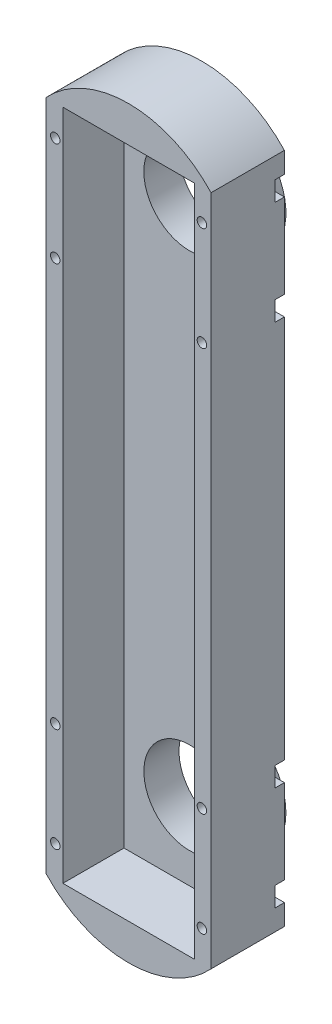
SolidWorks part; units mm, degrees
ref_plane "前视基准面" through (0, 0, 0) normal (0, 0, 1) x (1, 0, 0)
ref_plane "上视基准面" through (0, 0, 0) normal (0, 1, 0) x (1, 0, 0)
ref_plane "右视基准面" through (0, 0, 0) normal (1, 0, 0) x (0, 0, -1)
sketch "草图1" plane through (0, 0, 0) normal (0, 0, 1) x (1, 0, 0)
  line L1 (-27, 110) -> (27, 110)
  line L2 (-27, 110) -> (-27, -110)
  line L3 (-27, -110) -> (27, -110)
  line L4 (27, 110) -> (27, -110)
  line L5 (0, -110) -> (0, 110) construction
  line L6 (-27, 0) -> (27, 0) construction
  point P0 (0, 0)
  dimension "D1" = 220
  dimension "D2" = 54
extrude "凸台-拉伸1" add sketch "草图1" along normal blind 24
sketch "草图2" plane through (0, 0, 24) normal (0, 0, 1) x (1, 0, 0)
  line L0 (-27, 110) -> (-27, -110) construction
  line L1 (27, 110) -> (-27, 110) construction
  line L3 (-24, 100) -> (24, 100) construction
  line L5 (0, 0) -> (-70.719, 0) construction
  circle A0 centre (-24, 100) radius 1.55
  circle A1 centre (24, 100) radius 1.55
  circle A2 centre (24, 66) radius 1.55
  circle A3 centre (-24, 66) radius 1.55
  circle A4 centre (24, -100) radius 1.55
  circle A5 centre (24, -66) radius 1.55
  circle A6 centre (-24, -66) radius 1.55
  circle A7 centre (-24, -100) radius 1.55
  dimension "D1" = 3.1
  dimension "D6" = 48
  dimension "D2" = 3
  dimension "D3" = 10
  dimension "D7" = 34
  dimension "D4" = 2
  dimension "D5" = 2
extrude "切除-拉伸1" cut sketch "草图2" against normal through all
sketch "草图3" plane through (0, 0, 24) normal (0, 0, 1) x (1, 0, 0)
  line L0 (27, 110) -> (-27, 110) construction
  line L1 (-27, 110) -> (27, 110)
  line L2 (-27, -110) -> (27, -110) construction
  line L3 (-27, -110) -> (27, -110)
  arc A1 (-27, 110) -> (27, 110) centre (0, 84.9952) cw
  arc A2 (-27, -110) -> (27, -110) centre (0, -84.9952) ccw
  dimension "D1" = 36.8
extrude "凸台-拉伸2" add sketch "草图3" against normal up to surface (24 mm away) up to face at (22.45, -100, 0)
sketch "草图5" plane through (0, 0, 24) normal (0, 0, 1) x (1, 0, 0)
  line L0 (21.5, 110) -> (21.5, -110)
  line L2 (21.5, -110) -> (-21.5, -110)
  line L3 (-21.5, -110) -> (-21.5, 110)
  line L4 (0, 110) -> (0, -34.0506) construction
  line L5 (-21.5, 110) -> (21.5, 110)
  line L6 (0, 0) -> (-48.8779, 0) construction
  dimension "D1" = 220
  dimension "D2" = 43
extrude "切除-拉伸3" cut sketch "草图5" against normal blind 20
sketch "草图6" plane through (0, 0, 0) normal (0, 0, -1) x (-1, 0, 0)
  line L0 (-27, 69.2) -> (-24, 69.2)
  line L1 (-27, -110) -> (-27, 110) construction
  line L2 (-24, 62.8) -> (-27, 62.8)
  line L3 (-27, 69.2) -> (-27, 62.8)
  line L4 (-27, 103.2) -> (-27, 96.8)
  line L5 (-24, 96.8) -> (-27, 96.8)
  line L6 (-27, 103.2) -> (-24, 103.2)
  line L7 (-27, 69.2) -> (-27, 103.2) construction
  line L8 (0, 40.7864) -> (0, -44.4319) construction
  line L9 (27, 69.2) -> (24, 69.2)
  line L10 (24, 62.8) -> (27, 62.8)
  line L11 (27, 69.2) -> (27, 62.8)
  line L12 (27, 103.2) -> (24, 103.2)
  line L13 (24, 96.8) -> (27, 96.8)
  line L14 (27, 103.2) -> (27, 96.8)
  line L15 (0, 0) -> (-54.1071, 0) construction
  line L16 (27, -69.2) -> (27, -62.8)
  line L17 (24, -62.8) -> (27, -62.8)
  line L18 (27, -69.2) -> (24, -69.2)
  line L19 (27, -103.2) -> (27, -96.8)
  line L20 (24, -96.8) -> (27, -96.8)
  line L21 (27, -103.2) -> (24, -103.2)
  line L22 (-27, -103.2) -> (-24, -103.2)
  line L23 (-24, -96.8) -> (-27, -96.8)
  line L24 (-27, -103.2) -> (-27, -96.8)
  line L25 (-27, -69.2) -> (-24, -69.2)
  line L26 (-24, -62.8) -> (-27, -62.8)
  line L27 (-27, -69.2) -> (-27, -62.8)
  arc A0 (-24, 69.2) -> (-24, 62.8) centre (-24, 66) cw
  circle A1 centre (-24, 66) radius 1.55 construction
  arc A2 (-24, 103.2) -> (-24, 96.8) centre (-24, 100) cw
  arc A3 (24, 69.2) -> (24, 62.8) centre (24, 66) ccw
  arc A4 (24, 103.2) -> (24, 96.8) centre (24, 100) ccw
  arc A5 (24, -69.2) -> (24, -62.8) centre (24, -66) cw
  arc A6 (24, -103.2) -> (24, -96.8) centre (24, -100) cw
  arc A7 (-24, -103.2) -> (-24, -96.8) centre (-24, -100) ccw
  arc A8 (-24, -69.2) -> (-24, -62.8) centre (-24, -66) ccw
  dimension "D1" = 3.2
  dimension "D3" = 34
  dimension "D2" = 2
extrude "切除-拉伸4" cut sketch "草图6" against normal blind 3
sketch "草图7" plane through (0, 0, 0) normal (0, 0, -1) x (-1, 0, 0)
  line L0 (-27, 110) -> (27, 110) construction
  line L1 (0, 0) -> (0, 29.7821) construction
  line L2 (-27, 103.2) -> (-27, 110) construction
  line L3 (27, 110) -> (27, 103.2) construction
  line L4 (0, 0) -> (-81.8231, 0) construction
  circle A1 centre (0, 85) radius 15
  circle A2 centre (0, -85) radius 15
  point P0 (0, 0)
  dimension "D2" = 30
  dimension "D1" = 25
extrude "切除-拉伸5" cut sketch "草图7" against normal through all
fillet "圆角1" [suppressed] radius 5
sketch "草图11" plane through (0, 0, 0) normal (0, 0, -1) x (-1, 0, 0)
  line L0 (0, 0) -> (-101.3892, 0) construction
  circle A0 centre (0, 85) radius 20
  circle A1 centre (0, 85) radius 15
  circle A2 centre (0, -85) radius 15
  circle A3 centre (0, -85) radius 20
  dimension "D1" = 40
  dimension "D2" = 30
extrude "凸台-拉伸3" add sketch "草图11" along normal blind 7.5
sketch "草图12" plane through (0, 0, 0) normal (0, 0, -1) x (-1, 0, 0)
  line L0 (0, 0) -> (57.2331, 0) construction
  circle A0 centre (0, 85) radius 21
  circle A1 centre (0, 85) radius 20
  circle A2 centre (0, -85) radius 20
  circle A3 centre (0, -85) radius 21
  dimension "D1" = 42
  dimension "D2" = 40
extrude "凸台-拉伸4" add sketch "草图12" along normal blind 0.5
